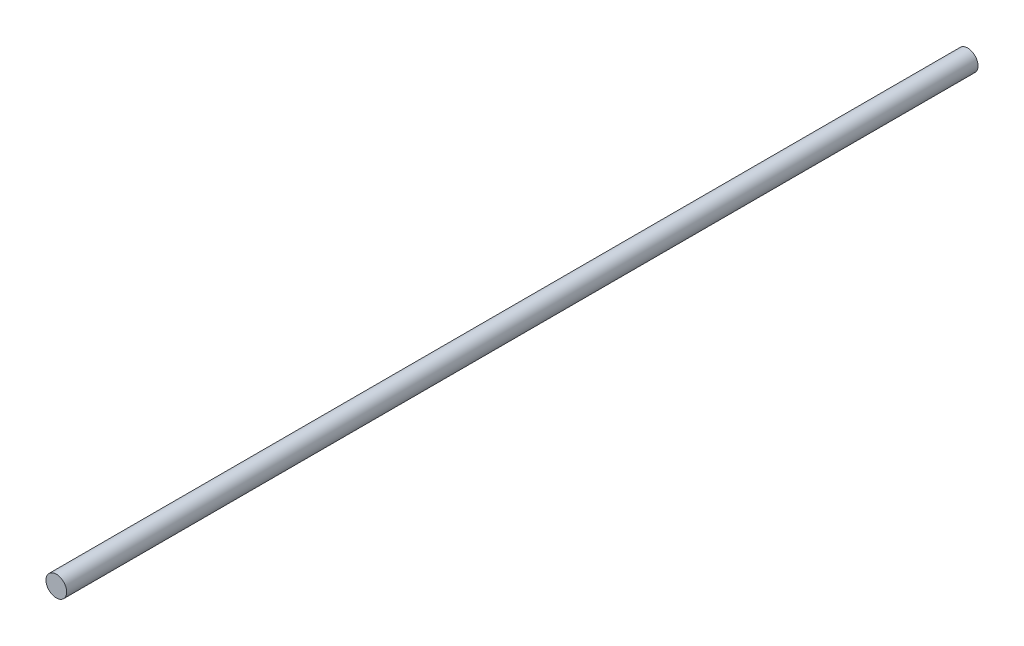
SolidWorks part; units mm, degrees
ref_plane "Front Plane" through (0, 0, 0) normal (0, 0, 1) x (1, 0, 0)
ref_plane "Top Plane" through (0, 0, 0) normal (0, 1, 0) x (1, 0, 0)
ref_plane "Right Plane" through (0, 0, 0) normal (1, 0, 0) x (0, 0, -1)
sketch "Sketch1" plane through (0, 0, 0) normal (0, 0, 1) x (1, 0, 0)
  circle A0 centre (0, 0) radius 3.9688
  dimension "D1" = 7.9375
extrude "Boss-Extrude1" add sketch "Sketch1" along normal blind 350
